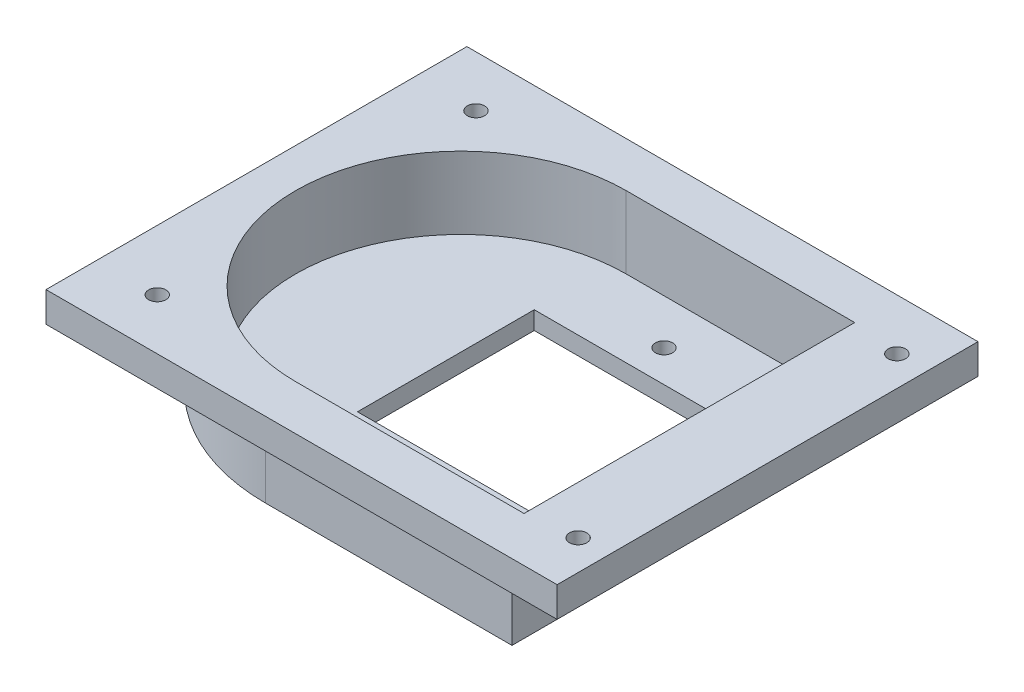
SolidWorks part; units mm, degrees
ref_plane "Alzado" through (0, 0, 0) normal (0, 0, 1) x (1, 0, 0)
ref_plane "Planta" through (0, 0, 0) normal (0, 1, 0) x (1, 0, 0)
ref_plane "Vista lateral" through (0, 0, 0) normal (1, 0, 0) x (0, 0, -1)
sketch "Croquis1" plane through (0, 0, 0) normal (0, 1, 0) x (1, 0, 0)
  line L1 (-42.5, 35) -> (42.5, 35)
  line L2 (-42.5, 35) -> (-42.5, -35)
  line L3 (-42.5, -35) -> (42.5, -35)
  line L4 (42.5, 35) -> (42.5, -35)
  line L5 (-42.5, 35) -> (42.5, -35) construction
  line L6 (-42.5, -35) -> (42.5, 35) construction
  point P0 (0, 0)
  dimension "D1" = 70
  dimension "D2" = 85
extrude "Saliente-Extruir1" add sketch "Croquis1" along normal blind 5
sketch "Croquis3" plane through (0, 0, 0) normal (0, -1, 0) x (-1, 0, 0)
  line L0 (-42.5, 35) -> (42.5, 35) construction
  line L3 (-42.5, -35) -> (-42.5, 35) construction
  line L4 (8.5, 32.5) -> (-32.5, 32.5)
  line L5 (-32.5, 32.5) -> (-32.5, -32.5)
  line L6 (-32.5, -32.5) -> (8.5, -32.5)
  arc A0 (8.5, -32.5) -> (8.5, 32.5) centre (8.5, 0) ccw
  dimension "D1" = 65
  dimension "D2" = 35
  dimension "D3" = 51
  dimension "D4" = 10
extrude "Saliente-Extruir2" add sketch "Croquis3" along normal blind 10
sketch "Croquis4" plane through (0, 5, 0) normal (0, 1, 0) x (1, 0, 0)
  line L0 (42.5, -35) -> (42.5, 35) construction
  line L1 (-42.5, -35) -> (42.5, -35) construction
  line L2 (-8.5, 27.5) -> (29.5, 27.5)
  line L3 (29.5, 27.5) -> (29.5, -27.5)
  line L4 (29.5, -27.5) -> (-8.5, -27.5)
  arc A0 (-8.5, 27.5) -> (-8.5, -27.5) centre (-8.5, 0) ccw
  dimension "D3" = 55
  dimension "D1" = 51
  dimension "D2" = 35
  dimension "D4" = 13
extrude "Cortar-Extruir1" cut sketch "Croquis4" against normal blind 12
sketch "Croquis6" plane through (0, -10, 0) normal (0, -1, 0) x (1, 0, 0)
  line L0 (32.5, -32.5) -> (32.5, 32.5) construction
  line L2 (-11, -14.7) -> (29.5, -14.7)
  line L3 (-11, -14.7) -> (-11, 14.7)
  line L4 (-11, 14.7) -> (29.5, 14.7)
  line L5 (29.5, -14.7) -> (29.5, 14.7)
  circle A0 centre (-8.5, 0) radius 13.8 construction
  circle A1 centre (-8.5, 0) radius 32.5 construction
  dimension "D1" = 27.6
  dimension "D2" = 29.4
  dimension "D5" = 14.7
  dimension "D3" = 2.5
  dimension "D4" = 3
extrude "Cortar-Extruir2" cut sketch "Croquis6" against normal through all
sketch "Croquis7" plane through (0, -10, 0) normal (0, -1, 0) x (-1, 0, 0)
  line L0 (47.9529, 0) -> (-47.9529, 0) construction
  line L1 (-42.5, -35) -> (-42.5, 35) construction
  circle A0 centre (-5.28, -20) radius 1.435
  circle A2 centre (-5.28, 20) radius 1.435
  dimension "D2" = 2.87
  dimension "D3" = 37.22
  dimension "D1" = 20
extrude "Cortar-Extruir3" cut sketch "Croquis7" against normal through all
sketch "Croquis8" plane through (0, 0, 0) normal (0, -1, 0) x (-1, 0, 0)
  line L0 (42.5, -35) -> (-42.5, -35) construction
  line L1 (42.5, 35) -> (42.5, -35) construction
  circle A0 centre (32.5, -26.5) radius 1.435
  circle A1 centre (-37.5, -26.5) radius 1.435
  circle A2 centre (-37.5, 26.5) radius 1.435
  circle A3 centre (32.5, 26.5) radius 1.435
  dimension "D1" = 2.87
  dimension "D2" = 8.5
  dimension "D3" = 10
  dimension "D4" = 2
  dimension "D5" = 2
extrude "Cortar-Extruir4" cut sketch "Croquis8" against normal through all
